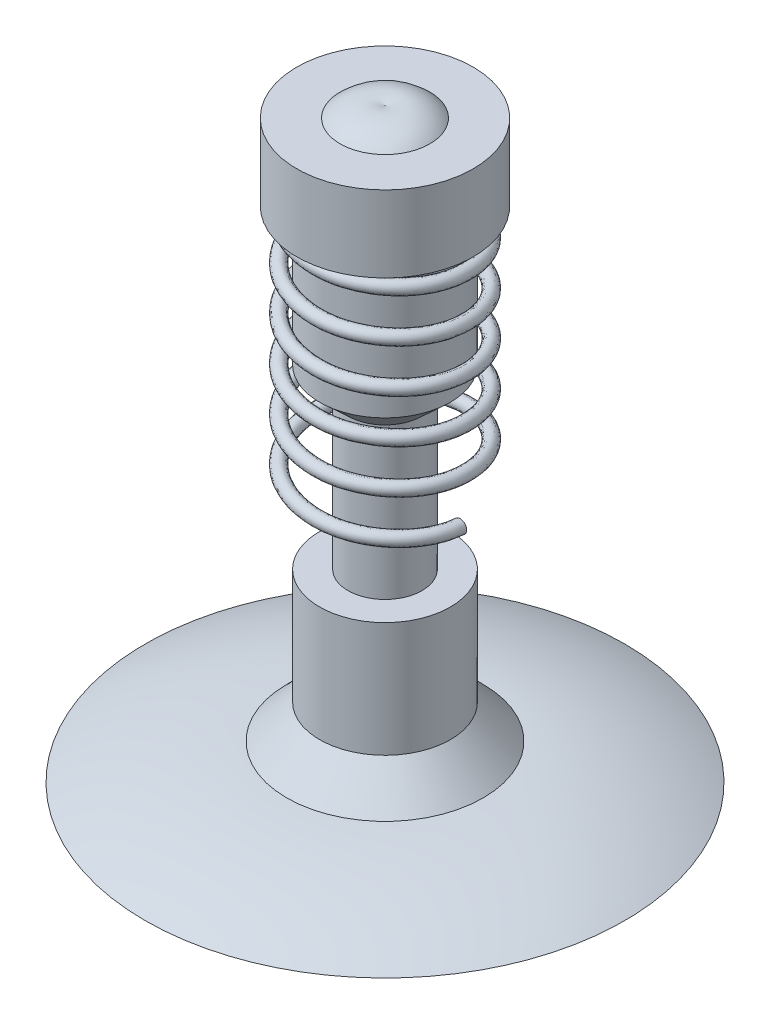
SolidWorks part; units mm, degrees
ref_plane "Front Plane" through (0, 0, 0) normal (0, 0, 1) x (1, 0, 0)
ref_plane "Top Plane" through (0, 0, 0) normal (0, 1, 0) x (1, 0, 0)
ref_plane "Right Plane" through (0, 0, 0) normal (1, 0, 0) x (0, 0, -1)
sketch "Sketch2" plane through (0, 0, 0) normal (0, 0, 1) x (1, 0, 0)
  line L0 (0, 0) -> (0, 2.69)
  line L1 (0, 0) -> (1.1, 0)
  line L2 (0.4509, 0.1634) -> (0.3, 0.3193)
  line L3 (0.3, 0.3193) -> (0.3, 0.8466)
  line L4 (0.3, 0.8466) -> (0.17, 0.8466)
  line L5 (0.17, 0.8466) -> (0.17, 1.54)
  line L6 (0.17, 1.54) -> (0.3, 1.66)
  line L7 (0.3, 1.66) -> (0.3, 2.29)
  line L8 (0.3, 2.29) -> (0.4047, 2.29)
  line L9 (0.4047, 2.29) -> (0.4047, 2.64)
  line L10 (0.4047, 2.64) -> (0.206, 2.64)
  arc A0 (1.1, 0) -> (0.4509, 0.1634) centre (0.4047, -1.3911) ccw
  arc A2 (0.206, 2.64) -> (0, 2.69) centre (0.063, 2.5003) ccw
  dimension "D1" = 2.69
  dimension "D2" = 1.1
  dimension "D3" = 0.35
  dimension "D4" = 0.63
  dimension "D5" = 0.17
  dimension "D6" = 0.3
  dimension "D7" = 0.3
  dimension "D8" = 0.05
revolve "Revolve1" add sketch "Sketch2" angle 360 about L0
sketch "Sketch3" plane through (0, 2.29, 0) normal (0, -1, 0) x (1, 0, 0)
  circle A0 centre (0, 0) radius 0.345
  dimension "D1" = 0.69
curve "Helix/Spiral1" pitch 0.2 height 1.1 turns 5.5
sketch "Sketch4" plane through (0, 0, 0) normal (0, 0, 1) x (1, 0, 0)
  circle A0 centre (0.345, 1.19) radius 0.03
  dimension "D1" = 0.06
sweep "Sweep1" add profiles "Sketch4" path "Helix/Spiral1"
